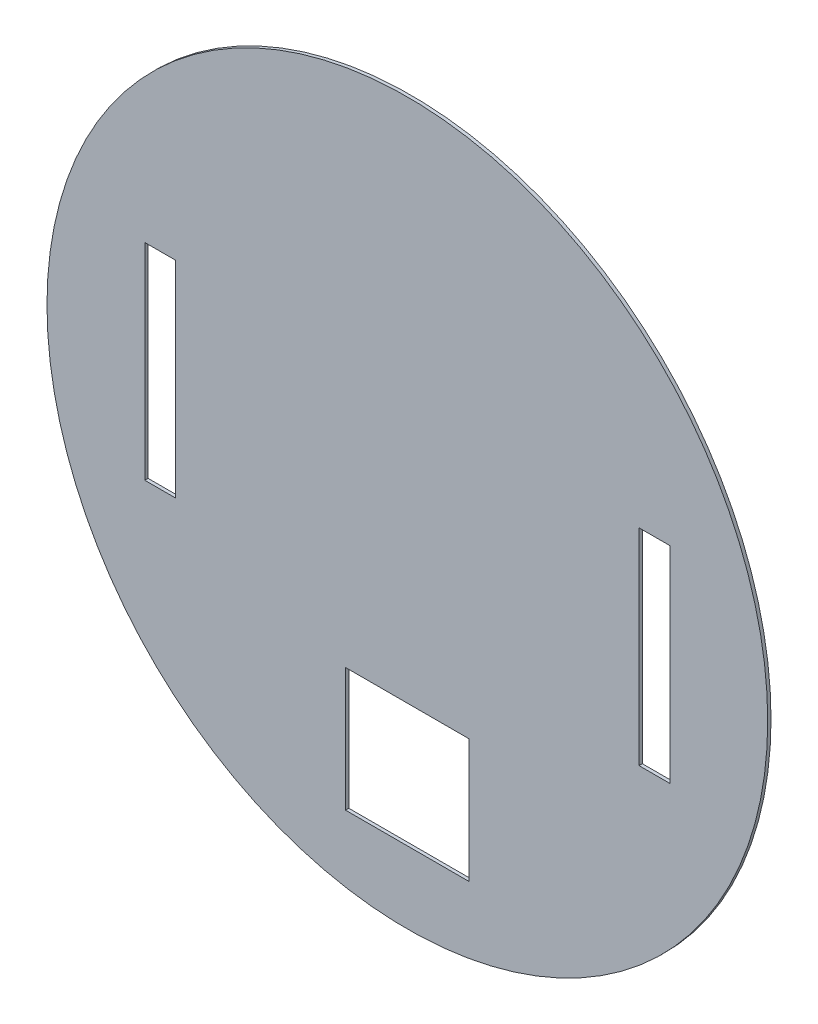
SolidWorks part; units mm, degrees
ref_plane "Front Plane" through (0, 0, 0) normal (0, 0, 1) x (1, 0, 0)
ref_plane "Top Plane" through (0, 0, 0) normal (0, 1, 0) x (1, 0, 0)
ref_plane "Right Plane" through (0, 0, 0) normal (1, 0, 0) x (0, 0, -1)
sketch "Sketch1" plane through (0, 0, 0) normal (0, 0, 1) x (1, 0, 0)
  circle A0 centre (0, 0) radius 175
  dimension "D1" = 350
extrude "Boss-Extrude1" add sketch "Sketch1" along normal blind 1.6
sketch "Sketch2" plane through (0, 0, 1.6) normal (0, 0, 1) x (1, 0, 0)
  line L0 (0, 0) -> (0, 175) construction
  line L1 (-127.5, 50) -> (-112.5, 50)
  line L2 (-127.5, 50) -> (-127.5, -50)
  line L3 (-127.5, -50) -> (-112.5, -50)
  line L4 (-112.5, 50) -> (-112.5, -50)
  line L5 (127.5, -50) -> (112.5, -50)
  line L6 (112.5, 50) -> (112.5, -50)
  line L7 (127.5, 50) -> (112.5, 50)
  line L8 (127.5, 50) -> (127.5, -50)
  circle A0 centre (0, 0) radius 175 construction
  point P4 (-112.5, 0)
  point P11 (-120, 50)
  dimension "D1" = 120
  dimension "D2" = 100
  dimension "D3" = 15
extrude "Cut-Extrude1" cut sketch "Sketch2" against normal blind 1.6
sketch "Sketch3" plane through (0, 0, 1.6) normal (0, 0, 1) x (1, 0, 0)
  line L1 (-30, -80) -> (30, -80)
  line L2 (-30, -80) -> (-30, -140)
  line L3 (-30, -140) -> (30, -140)
  line L4 (30, -80) -> (30, -140)
  point P4 (0, -80)
  dimension "D1" = 60
  dimension "D2" = 60
  dimension "D3" = 80
extrude "Cut-Extrude2" cut sketch "Sketch3" against normal through all
